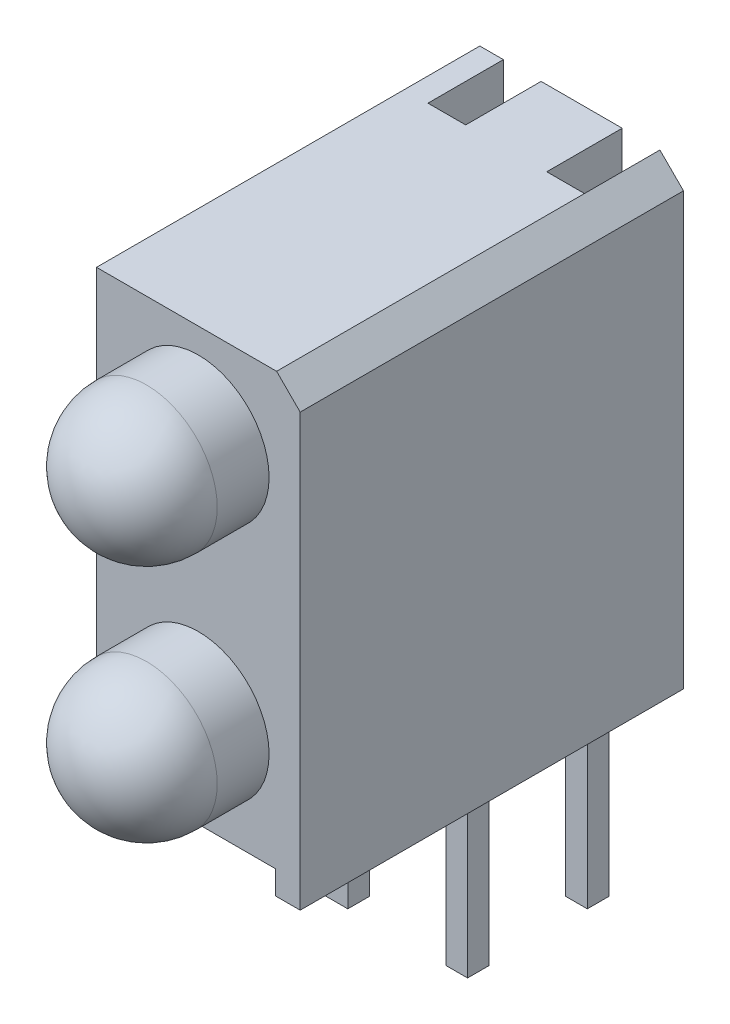
SolidWorks part; units mm, degrees
ref_plane "face" through (0, 0, 0) normal (0, 0, 1) x (1, 0, 0)
ref_plane "dessus" through (0, 0, 0) normal (0, 1, 0) x (1, 0, 0)
ref_plane "droite" through (0, 0, 0) normal (1, 0, 0) x (0, 0, -1)
sketch "Esquisse1" plane through (0, 0, 0) normal (0, 0, 1) x (1, 0, 0)
  line L0 (-3.8, 0) -> (-3.8, 0.5)
  line L1 (0, 0) -> (-0.52, 0)
  line L2 (0, 0) -> (0, 9.15)
  line L3 (-0.5, 9.65) -> (-4.32, 9.65)
  line L4 (-4.32, 0) -> (-4.32, 9.65)
  line L5 (-3.8, 0.5) -> (-0.52, 0.5)
  line L6 (-0.52, 0.5) -> (-0.52, 0)
  line L7 (-3.8, 0) -> (-4.32, 0)
  line L8 (0, 9.15) -> (-0.5, 9.65)
  point P2 (0, 9.65)
  dimension "D1" = 4.32
  dimension "D2" = 9.65
  dimension "D3" = 0.52
  dimension "D4" = 0.52
  dimension "D5" = 9.15
  dimension "D6" = 0.5
  dimension "D9" = 0.5
extrude "Extrusion1" add sketch "Esquisse1" along normal blind 8.13
sketch "Esquisse2" plane through (0, 9.65, 0) normal (0, 1, 0) x (1, 0, 0)
  line L0 (-0.5, 0) -> (-4.32, 0) construction
  line L1 (-0.5, 0) -> (-1.3, 0)
  line L2 (-3.82, 0) -> (-3.82, -1.6)
  line L3 (-3.82, -1.6) -> (-3.02, -1.6)
  line L4 (-3.02, -1.6) -> (-3.02, 0)
  line L5 (-0.5, 0) -> (-0.5, -1.6)
  line L6 (-0.5, -8.13) -> (-0.5, 0) construction
  line L7 (-0.5, -1.6) -> (-1.3, -1.6)
  line L8 (-1.3, -1.6) -> (-1.3, 0)
  line L9 (-4.32, -8.13) -> (-4.32, 0) construction
  line L10 (-3.02, 0) -> (-3.82, 0)
  dimension "D1" = 0.8
  dimension "D2" = 0.8
  dimension "D3" = 0.5
  dimension "D4" = 1.6
extrude "Extrusion2" cut sketch "Esquisse2" against normal blind 10.55
ref_plane "Plan1" through (0, -3.68, 0) normal (0, -1, 0) x (1, 0, 0)
sketch "Esquisse3" plane through (0, -3.68, 0) normal (0, -1, 0) x (1, 0, 0)
  line L0 (-3.02, 0) -> (-1.3, 0) construction
  line L1 (-0.66, 3.92) -> (-1.12, 3.92)
  line L2 (-0.66, 3.92) -> (-0.66, 3.46)
  line L3 (-0.66, 3.46) -> (-1.12, 3.46)
  line L4 (-1.12, 3.92) -> (-1.12, 3.46)
  line L5 (-3.2, 3.92) -> (-3.66, 3.92)
  line L6 (-3.2, 3.92) -> (-3.2, 3.46)
  line L7 (-3.2, 3.46) -> (-3.66, 3.46)
  line L8 (-3.66, 3.92) -> (-3.66, 3.46)
  line L9 (-3.8, 8.13) -> (-0.52, 8.13) construction
  line L10 (-3.2, 3.92) -> (-3.66, 3.46) construction
  line L11 (-0.66, 3.92) -> (-1.12, 3.46) construction
  line L13 (-2.16, 0) -> (-2.16, 8.13) construction
  line L15 (-3.2, 1.38) -> (-3.66, 0.92) construction
  line L16 (-3.66, 1.38) -> (-3.2, 1.38)
  line L17 (-3.66, 1.38) -> (-3.66, 0.92)
  line L18 (-3.66, 0.92) -> (-3.2, 0.92)
  line L19 (-3.2, 1.38) -> (-3.2, 0.92)
  line L20 (-1.12, 1.38) -> (-0.66, 1.38)
  line L21 (-1.12, 1.38) -> (-1.12, 0.92)
  line L22 (-1.12, 0.92) -> (-0.66, 0.92)
  line L23 (-0.66, 1.38) -> (-0.66, 0.92)
  line L24 (-0.66, 1.38) -> (-1.12, 0.92) construction
  point P8 (-3.43, 3.69)
  point P15 (-0.89, 3.69)
  point P24 (-0.89, 1.15)
  point P25 (-3.43, 1.15)
  dimension "D1" = 0.46
  dimension "D2" = 2.54
  dimension "D3" = 1.27
  dimension "D4" = 4.44
sketch "Esquisse4" plane through (0, 0.5, 0) normal (0, -1, 0) x (1, 0, 0)
  line L0 (-3.02, 1.6) -> (-3.02, 4.14)
  line L1 (-3.02, 4.14) -> (-3.8, 4.14)
  line L2 (-3.8, 8.13) -> (-3.8, 1.6) construction
  line L3 (-3.8, 4.14) -> (-3.8, 1.6)
  line L4 (-3.8, 1.6) -> (-3.02, 1.6)
  line L5 (-1.3, 1.6) -> (-1.3, 4.14)
  line L6 (-1.3, 4.14) -> (-0.52, 4.14)
  line L7 (-0.52, 8.13) -> (-0.52, 1.6) construction
  line L8 (-0.52, 4.14) -> (-0.52, 1.6)
  line L9 (-0.52, 1.6) -> (-1.3, 1.6)
  line L10 (-3.02, 1.6) -> (-3.02, 0) construction
  line L11 (-3.2, 3.92) -> (-3.66, 3.92) construction
  line L12 (-1.12, 1.38) -> (-0.66, 1.38) construction
  dimension "D1" = 2.54
  dimension "D2" = 0.22
  dimension "D3" = 0.22
extrude "Extrusion3" cut sketch "Esquisse4" against normal blind 0.5
ref_plane "Plan2" through (0, 7.85, 0) normal (0, -1, 0) x (1, 0, 0)
sketch "Esquisse5" plane through (0, -3.68, 0) normal (0, -1, 0) x (1, 0, 0)
  line L0 (-3.2, 3.92) -> (-3.66, 3.92) construction
  line L1 (-3.66, 3.92) -> (-3.66, 3.46) construction
  line L2 (-3.2, 3.46) -> (-3.66, 3.46) construction
  line L3 (-3.2, 3.92) -> (-3.2, 3.46) construction
  line L4 (-1.12, 3.92) -> (-1.12, 3.46) construction
  line L5 (-0.66, 3.92) -> (-1.12, 3.92) construction
  line L6 (-0.66, 3.92) -> (-0.66, 3.46) construction
  line L7 (-0.66, 3.46) -> (-1.12, 3.46) construction
  line L8 (-3.2, 3.92) -> (-3.66, 3.92)
  line L9 (-3.66, 3.92) -> (-3.66, 3.46)
  line L10 (-3.2, 3.46) -> (-3.66, 3.46)
  line L11 (-3.2, 3.92) -> (-3.2, 3.46)
  line L12 (-1.12, 3.92) -> (-1.12, 3.46)
  line L13 (-0.66, 3.92) -> (-1.12, 3.92)
  line L14 (-0.66, 3.92) -> (-0.66, 3.46)
  line L15 (-0.66, 3.46) -> (-1.12, 3.46)
extrude "Extrusion4" add sketch "Esquisse5" against normal up to surface (4.68 mm away) up to face at (-0.91, 1, 2.87)
sketch "Esquisse6" plane through (0, -3.68, 0) normal (0, -1, 0) x (1, 0, 0)
  line L0 (-3.66, 1.38) -> (-3.2, 1.38) construction
  line L1 (-3.66, 1.38) -> (-3.66, 0.92) construction
  line L2 (-3.66, 0.92) -> (-3.2, 0.92) construction
  line L3 (-3.2, 1.38) -> (-3.2, 0.92) construction
  line L4 (-1.12, 1.38) -> (-1.12, 0.92) construction
  line L5 (-1.12, 1.38) -> (-0.66, 1.38) construction
  line L6 (-0.66, 1.38) -> (-0.66, 0.92) construction
  line L7 (-1.12, 0.92) -> (-0.66, 0.92) construction
  line L8 (-3.66, 1.38) -> (-3.2, 1.38)
  line L9 (-3.66, 1.38) -> (-3.66, 0.92)
  line L10 (-3.66, 0.92) -> (-3.2, 0.92)
  line L11 (-3.2, 1.38) -> (-3.2, 0.92)
  line L12 (-1.12, 1.38) -> (-1.12, 0.92)
  line L13 (-1.12, 1.38) -> (-0.66, 1.38)
  line L14 (-0.66, 1.38) -> (-0.66, 0.92)
  line L15 (-1.12, 0.92) -> (-0.66, 0.92)
extrude "Extrusion5" add sketch "Esquisse6" against normal up to surface (11.53 mm away) separate body up to plane "Plan2"
sketch "Esquisse7" plane through (0, 0, 1.38) normal (0, 0, 1) x (1, 0, 0)
  line L0 (-0.66, 7.85) -> (-1.12, 7.85) construction
  line L1 (-0.66, 7.85) -> (-1.12, 7.85)
  line L2 (-3.2, 7.85) -> (-3.66, 7.85) construction
  line L3 (-3.2, 7.85) -> (-3.66, 7.85)
  line L4 (-0.66, 7.85) -> (-0.66, -3.68) construction
  line L5 (-0.66, 7.85) -> (-0.66, 7.39)
  line L6 (-1.12, 7.85) -> (-1.12, -3.68) construction
  line L7 (-1.12, 7.85) -> (-1.12, 7.39)
  line L8 (-3.2, 7.85) -> (-3.2, -3.68) construction
  line L9 (-3.2, 7.85) -> (-3.2, 7.39)
  line L10 (-3.66, 7.85) -> (-3.66, -3.68) construction
  line L11 (-3.66, 7.85) -> (-3.66, 7.39)
  line L12 (-0.66, 7.39) -> (-1.12, 7.39)
  line L13 (-3.2, 7.39) -> (-3.66, 7.39)
extrude "Extrusion6" add sketch "Esquisse7" along normal up to surface (0.22 mm away) up to face at (-0.7733, 3.55, 1.6)
ref_plane "Plan3" through (-2.16, 0, 0) normal (1, 0, 0) x (0, 0, -1)
sketch "Esquisse9" plane through (-2.16, 0, 0) normal (1, 0, 0) x (0, 0, -1)
  line L0 (-13.7412, 2.54) -> (-5.2028, 2.54) construction
  line L1 (-8.13, 0) -> (0, 0) construction
  line L2 (-9.23, 1.04) -> (-8.13, 1.04)
  line L3 (-8.13, 1.04) -> (-8.13, 2.54)
  line L4 (-8.13, 2.54) -> (-10.73, 2.54)
  line L5 (-8.13, 0) -> (-8.13, 9.15) construction
  arc A0 (-10.73, 2.54) -> (-9.23, 1.04) centre (-9.23, 2.54) ccw
  dimension "D2" = 3
  dimension "D1" = 2.54
  dimension "D3" = 2.6
revolve "Révolution1" add sketch "Esquisse9" angle 360 about L0
sketch "Esquisse10" plane through (-2.16, 0, 0) normal (1, 0, 0) x (0, 0, -1)
  line L0 (-13.1299, 7.62) -> (-5.4893, 7.62) construction
  line L2 (-8.33, 2.54) -> (-11.03, 2.54) construction
  line L3 (-9.23, 6.12) -> (-8.13, 6.12)
  line L4 (-8.13, 6.12) -> (-8.13, 7.62)
  line L5 (-8.13, 7.62) -> (-10.73, 7.62)
  line L6 (-8.13, 0) -> (-8.13, 9.15) construction
  arc A0 (-10.73, 7.62) -> (-9.23, 6.12) centre (-9.23, 7.62) ccw
  dimension "D2" = 3
  dimension "D1" = 5.08
  dimension "D3" = 2.6
revolve "Révolution2" add sketch "Esquisse10" angle 360 about L0
